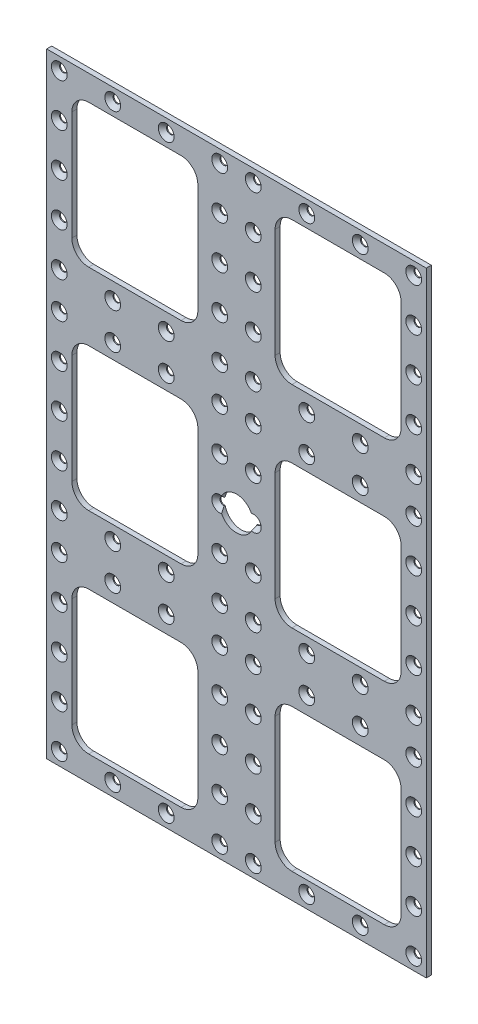
SolidWorks part; units mm, degrees
material "6061-T6 (SS)"
ref_plane "Alzado" through (0, 0, 0) normal (0, 0, 1) x (1, 0, 0)
ref_plane "Planta" through (0, 0, 0) normal (0, 1, 0) x (1, 0, 0)
ref_plane "Vista lateral" through (0, 0, 0) normal (1, 0, 0) x (0, 0, -1)
sketch "Sketch1" plane through (0, 0, 0) normal (0, 0, 1) x (1, 0, 0)
  line L1 (-113, 183) -> (113, 183)
  line L2 (-113, 183) -> (-113, -183)
  line L3 (-113, -183) -> (113, -183)
  line L4 (113, 183) -> (113, -183)
  line L5 (-113, 183) -> (113, -183) construction
  line L6 (-113, -183) -> (113, 183) construction
  point P0 (0, 0)
  dimension "D1" = 366
  dimension "D2" = 226
extrude "Boss-Extrude1" add sketch "Sketch1" along normal blind 3
sketch "Sketch2" plane through (0, 0, 0) normal (0, 0, 1) x (1, 0, 0)
  line L0 (0, 186.1376) -> (0, -191.1438) construction
  line L1 (-164.2926, 0) -> (162.9273, 0) construction
  line L2 (113, 183) -> (-113, 183) construction
  line L3 (-98, 168) -> (-23, 168)
  line L4 (-98, 168) -> (-98, 83)
  line L5 (-98, 83) -> (-23, 83)
  line L6 (-23, 168) -> (-23, 83)
  line L7 (-98, 168) -> (-23, 83) construction
  line L8 (-98, 83) -> (-23, 168) construction
  line L9 (-113, 183) -> (-113, -183) construction
  point P5 (-60.5, 125.5)
  dimension "D1" = 15
  dimension "D2" = 15
  dimension "D3" = 75
  dimension "D4" = 85
extrude "Cut-Extrude4" cut sketch "Sketch2" along normal through all
fillet "Fillet1" radius 10 4 edges at (-23, 83, 1.5) (-23, 168, 1.5) (-98, 83, 1.5) (-98, 168, 1.5)
pattern_linear "LPattern1" count 3 spacing 125.5 along (0, -1, 0) count 2 spacing 121 along (1, 0, 0) of "Cut-Extrude4", "Fillet1"
sketch "Sketch12" plane through (0, 0, 3) normal (0, 0, 1) x (1, 0, 0)
  line L0 (113, 183) -> (-113, 183) construction
  line L1 (-113, 183) -> (-113, -183) construction
  point P0 (-105.5, 175.5)
  dimension "D1" = 7.5
  dimension "D2" = 7.5
hole_wizard "CSK for M4 Flat Head Machine Screw4" positions "Sketch12" profile "Sketch13" countersink size "M4" standard "ANSI Metric" end condition through all
sketch "Sketch13" plane through (-105.5, 175.5, 3) normal (1, 0, 0) x (0, -1, 0)
  line L0 (0, 0) -> (0, 3)
  line L1 (0, 3) -> (2.25, 3)
  line L2 (2.25, 3) -> (2.25, 2.45)
  line L3 (2.25, 2.45) -> (4.7, 0)
  line L5 (4.7, 0) -> (0, 0)
  line L6 (-2.25, 2.45) -> (-4.7, 0) construction
  line L11 (0, -6.35) -> (0, 107.95) construction
  dimension "Thru Hole Dia." = 4.5
  dimension "Thru Hole Depth" = 3
  dimension "Near C'Sink Dia." = 9.4
  dimension "Near C'Sink Angle" = 90
sketch "Sketch14" plane through (0, 0, 3) normal (0, 0, 1) x (1, 0, 0)
  line L0 (0, 183) -> (0, -183) construction
  line L1 (113, 183) -> (-113, 183) construction
  line L2 (-113, -183) -> (113, -183) construction
  line L3 (-113, 62.75) -> (113, 62.75) construction
  line L4 (-113, 183) -> (-113, -183) construction
  line L5 (113, -183) -> (113, 183) construction
  line L6 (-113, -62.75) -> (113, -62.75) construction
  line L7 (-88, 83) -> (-33, 83) construction
  line L8 (-33, 42.5) -> (-88, 42.5) construction
  line L9 (-88, -42.5) -> (-33, -42.5) construction
  line L10 (-33, -83) -> (-88, -83) construction
pattern_linear "LPattern7" count 4 spacing 31.8333 along (1, 0, 0) count 5 spacing 25.6562 along (0, -1, 0) skipping (1, 1), (1, 2), (1, 3), (2, 1), (2, 2), (2, 3) of "CSK for M4 Flat Head Machine Screw4"
pattern_linear "LPattern8" count 3 spacing 124.1875 along (0, -1, 0) of "LPattern7", "CSK for M4 Flat Head Machine Screw4"
mirror "Mirror1" about plane through (0, 0, 0) normal (1, 0, 0) of "LPattern8", "CSK for M4 Flat Head Machine Screw4", "LPattern7"
sketch "Sketch15" plane through (0, 0, 3) normal (0, 0, 1) x (1, 0, 0)
  circle A0 centre (0, 0) radius 10
  dimension "D1" = 20
extrude "Cut-Extrude5" cut sketch "Sketch15" against normal up to next
